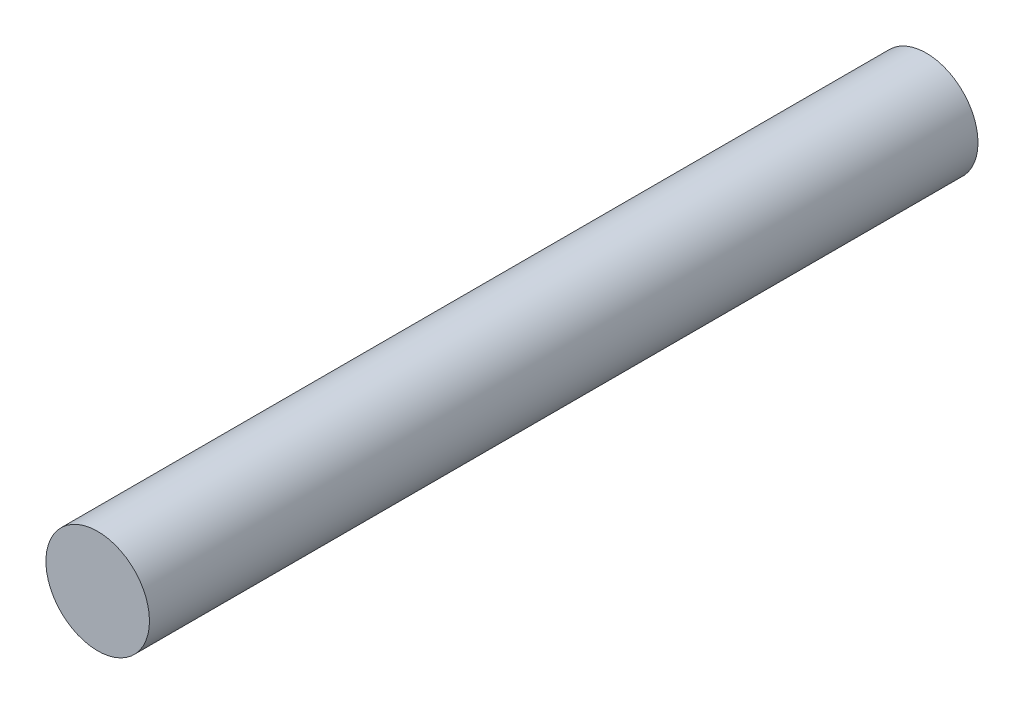
SolidWorks part; units mm, degrees
ref_plane "Front Plane" through (0, 0, 0) normal (0, 0, 1) x (1, 0, 0)
ref_plane "Top Plane" through (0, 0, 0) normal (0, 1, 0) x (1, 0, 0)
ref_plane "Right Plane" through (0, 0, 0) normal (1, 0, 0) x (0, 0, -1)
sketch "Sketch1" plane through (0, 0, 0) normal (0, 0, 1) x (1, 0, 0)
  circle A0 centre (0, 0) radius 1.5
  dimension "D1" = 3
extrude "Boss-Extrude1" add sketch "Sketch1" along normal blind 24
